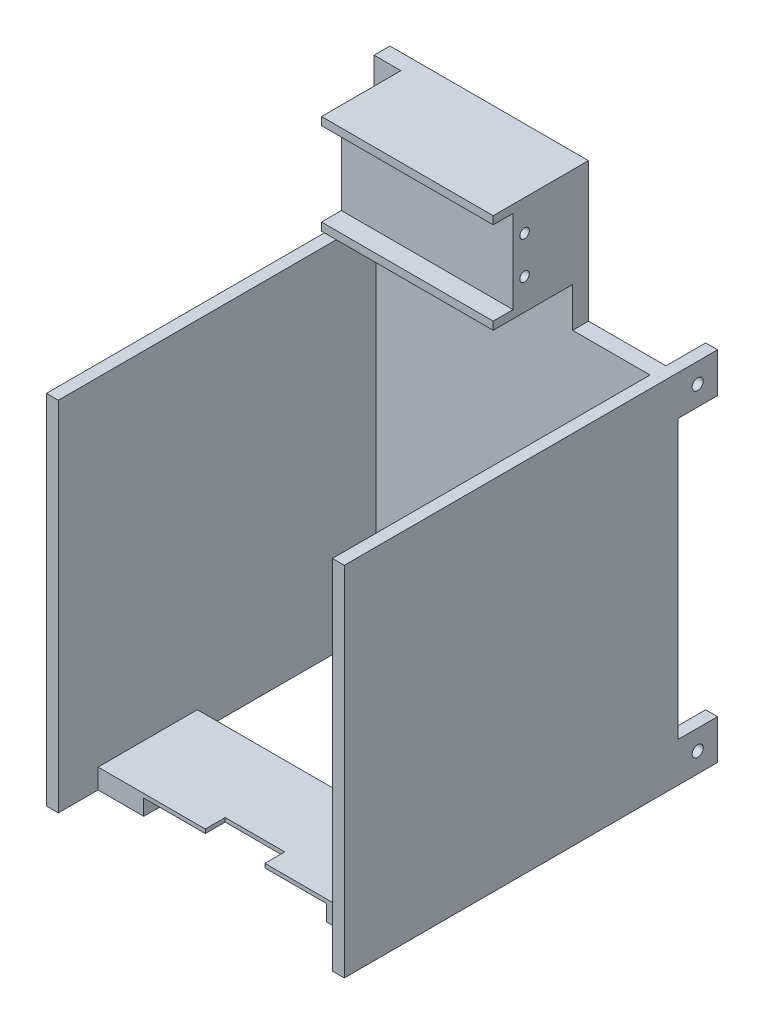
SolidWorks part; units mm, degrees
ref_plane "前基準面" through (0, 0, 0) normal (0, 0, 1) x (1, 0, 0)
ref_plane "上基準面" through (0, 0, 0) normal (0, 1, 0) x (1, 0, 0)
ref_plane "右基準面" through (0, 0, 0) normal (1, 0, 0) x (0, 0, -1)
sketch "草圖1" plane through (0, 0, 0) normal (0, 0, 1) x (1, 0, 0)
  line L0 (0, -55) -> (0, 55) construction
  line L1 (-37.5, 45) -> (-35, 45)
  line L2 (-37.5, 45) -> (-37.5, -45)
  line L3 (-37.5, -45) -> (37.5, -45)
  line L4 (37.5, 45) -> (37.5, -45)
  line L5 (55, 0) -> (-55, 0) construction
  line L6 (15, 45) -> (37.5, 45)
  line L8 (-35, 45) -> (-35, 80)
  line L9 (-35, 80) -> (15, 80)
  line L10 (15, 45) -> (15, 80)
  dimension "D1" = 75
  dimension "D2" = 90
  dimension "D3" = 37.5
  dimension "D4" = 45
  dimension "D5" = 35
  dimension "D6" = 35
  dimension "D7" = 50
extrude "填料-伸長1" add sketch "草圖1" along normal blind 4 contours L1 L10 L9 L8 | L4 L1 L2 L3
sketch "草圖3" plane through (0, 0, 4) normal (0, 0, 1) x (1, 0, 0)
  line L0 (-35, 80) -> (15, 80) construction
  line L1 (-28.2355, 57) -> (15, 57)
  line L2 (-28.2355, 57) -> (-28.2355, 55)
  line L3 (-28.2355, 55) -> (15, 55)
  line L4 (15, 57) -> (15, 55)
  line L5 (-28.2355, 80) -> (15, 80)
  line L6 (-28.2355, 80) -> (-28.2355, 78)
  line L7 (-28.2355, 78) -> (15, 78)
  line L8 (15, 80) -> (15, 78)
  dimension "D1" = 2
  dimension "D2" = 2
  dimension "D3" = 21
extrude "填料-伸長2" add sketch "草圖3" along normal blind 20
sketch "草圖4" plane through (0, 0, 4) normal (0, 0, 1) x (1, 0, 0)
  line L1 (-28.2355, 78) -> (15, 78)
  line L2 (-28.2355, 78) -> (-28.2355, 57)
  line L3 (-28.2355, 57) -> (15, 57)
  line L4 (15, 78) -> (15, 57)
extrude "填料-伸長3" add sketch "草圖4" along normal blind 15
sketch "草圖8" plane through (0, 0, 0) normal (0, 0, -1) x (-1, 0, 0)
  line L1 (-37.5, 45) -> (-34.5, 45)
  line L2 (-37.5, 45) -> (-37.5, 35)
  line L3 (-37.5, 35) -> (-34.5, 35)
  line L4 (-34.5, 45) -> (-34.5, 35)
  line L5 (37.5, 45) -> (34.5, 45)
  line L6 (37.5, 45) -> (37.5, 35)
  line L7 (37.5, 35) -> (34.5, 35)
  line L8 (34.5, 45) -> (34.5, 35)
  line L9 (37.5, -45) -> (34.5, -45)
  line L10 (37.5, -45) -> (37.5, -35)
  line L11 (37.5, -35) -> (34.5, -35)
  line L12 (34.5, -45) -> (34.5, -35)
  line L13 (-37.5, -45) -> (-34.5, -45)
  line L14 (-37.5, -45) -> (-37.5, -35)
  line L15 (-37.5, -35) -> (-34.5, -35)
  line L16 (-34.5, -45) -> (-34.5, -35)
  dimension "D1" = 3
  dimension "D2" = 3
  dimension "D3" = 10
  dimension "D4" = 10
  dimension "D5" = 10
  dimension "D6" = 3
  dimension "D7" = 10
  dimension "D8" = 3
extrude "填料-伸長4" add sketch "草圖8" along normal blind 10
sketch "草圖10" plane through (37.5, 0, 0) normal (1, 0, 0) x (0, 0, -1)
  line L0 (10, 45) -> (10, 35) construction
  line L1 (-4, 45) -> (10, 45) construction
  line L2 (10, -35) -> (0, -35) construction
  line L3 (10, -35) -> (10, -45) construction
  circle A0 centre (5, 40) radius 1.4
  circle A1 centre (5, -40) radius 1.4
  dimension "D1" = 2.8
  dimension "D4" = 2.8
  dimension "D2" = 5
  dimension "D3" = 5
  dimension "D5" = 5
  dimension "D6" = 5
extrude "除料-伸長1" cut sketch "草圖10" against normal blind 83
sketch "草圖11" plane through (0, 0, 4) normal (0, 0, 1) x (1, 0, 0)
  line L1 (-37.5, 45) -> (-34.5, 45)
  line L2 (-37.5, 45) -> (-37.5, -45)
  line L3 (-37.5, -45) -> (-34.5, -45)
  line L4 (-34.5, 45) -> (-34.5, -45)
  line L5 (37.5, 45) -> (34.5, 45)
  line L6 (37.5, 45) -> (37.5, -45)
  line L7 (37.5, -45) -> (34.5, -45)
  line L8 (34.5, 45) -> (34.5, -45)
extrude "填料-伸長5" add sketch "草圖11" along normal blind 80
sketch "草圖12" plane through (0, -45, 0) normal (0, -1, 0) x (1, 0, 0)
  line L2 (-36.2277, 74) -> (-36.2277, 49)
  line L3 (-36.2277, 49) -> (36.4801, 49)
  line L4 (36.4801, 74) -> (36.4801, 49)
  line L6 (-36.2277, 74) -> (36.4801, 74)
  dimension "D1" = 25
extrude "填料-伸長6" add sketch "草圖12" against normal blind 5
sketch "草圖13" plane through (0, -45, 0) normal (0, -1, 0) x (1, 0, 0)
  line L0 (34.5, 74) -> (-34.5, 74) construction
  line L1 (-23, 74) -> (23, 74)
  line L2 (-23, 74) -> (-23, 54)
  line L3 (-23, 54) -> (23, 54)
  line L4 (23, 74) -> (23, 54)
  line L5 (0, -18.7) -> (0, 18.7) construction
  dimension "D1" = 20
  dimension "D2" = 46
  dimension "D3" = 23
extrude "除料-伸長2" cut sketch "草圖13" against normal blind 4
sketch "草圖14" plane through (0, -41, 0) normal (0, -1, 0) x (1, 0, 0)
  line L0 (23, 74) -> (-23, 74) construction
  line L1 (-7.5, 74) -> (7.5, 74)
  line L2 (-7.5, 74) -> (-7.5, 69)
  line L3 (-7.5, 69) -> (7.5, 69)
  line L4 (7.5, 74) -> (7.5, 69)
  line L6 (0, -18.7) -> (0, 18.7) construction
  dimension "D1" = 5
  dimension "D2" = 15
  dimension "D3" = 7.5
extrude "除料-伸長3" cut sketch "草圖14" against normal up to next
sketch "草圖15" plane through (15, 0, 0) normal (1, 0, 0) x (0, 0, -1)
  line L0 (-24, 78) -> (-19, 78) construction
  line L1 (-19, 57) -> (-19, 78) construction
  line L3 (-24, 57) -> (-19, 57) construction
  circle A0 centre (-16.1, 72.2) radius 1.2
  circle A1 centre (-16.1, 62.8) radius 1.2
  point P10 (-21.436, 57)
  dimension "D1" = 5.8
  dimension "D2" = 2.9
  dimension "D3" = 2.9
  dimension "D4" = 5.8
extrude "除料-伸長4" cut sketch "草圖15" against normal blind 10
